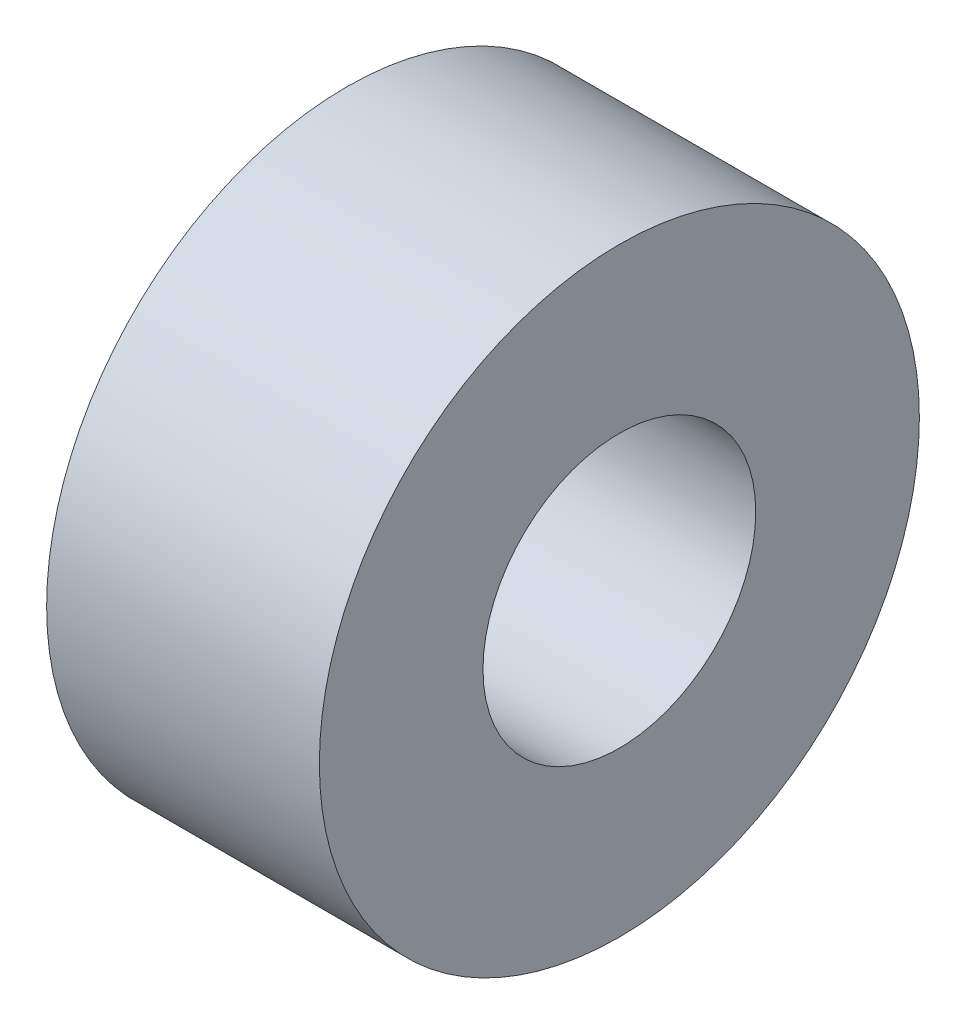
SolidWorks part; units mm, degrees
material "6061-T6 (SS)"
ref_plane "Front Plane" through (0, 0, 0) normal (0, 0, 1) x (1, 0, 0)
ref_plane "Top Plane" through (0, 0, 0) normal (0, 1, 0) x (1, 0, 0)
ref_plane "Right Plane" through (0, 0, 0) normal (1, 0, 0) x (0, 0, -1)
sketch "Sketch1" plane through (0, 0, 0) normal (1, 0, 0) x (0, 0, -1)
  circle A0 centre (0, 0) radius 8.7312
  circle A1 centre (0, 0) radius 3.9688
  dimension "D1" = 17.4625
  dimension "D2" = 7.9375
extrude "Boss-Extrude1" add sketch "Sketch1" along normal mid plane 7.9375
